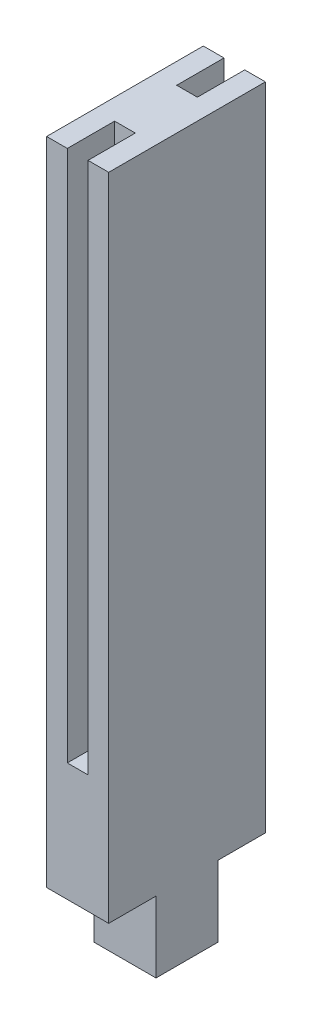
SolidWorks part; units mm, degrees
ref_plane "Front Plane" through (0, 0, 0) normal (0, 0, 1) x (1, 0, 0)
ref_plane "Top Plane" through (0, 0, 0) normal (0, 1, 0) x (1, 0, 0)
ref_plane "Right Plane" through (0, 0, 0) normal (1, 0, 0) x (0, 0, -1)
sketch "Sketch1" plane through (0, 0, 0) normal (0, 1, 0) x (1, 0, 0)
  line L1 (-2.625, -2.625) -> (2.625, -2.625)
  line L2 (-2.625, -2.625) -> (-2.625, 2.625)
  line L3 (-2.625, 2.625) -> (2.625, 2.625)
  line L4 (2.625, -2.625) -> (2.625, 2.625)
  line L5 (-2.625, -2.625) -> (2.625, 2.625) construction
  line L6 (-2.625, 2.625) -> (2.625, -2.625) construction
  point P0 (0, 0)
  dimension "D1" = 5.25
  dimension "D2" = 5.25
extrude "Boss-Extrude1" add sketch "Sketch1" along normal blind 6
sketch "Sketch2" plane through (0, 6, 0) normal (0, 1, 0) x (1, 0, 0)
  line L1 (-2.625, 2.625) -> (2.625, 2.625)
  line L2 (-2.625, 2.625) -> (-2.625, -6.625)
  line L3 (-2.625, -6.625) -> (2.625, -6.625)
  line L4 (2.625, 2.625) -> (2.625, -6.625)
  dimension "D1" = 5.25
  dimension "D2" = 9.25
extrude "Boss-Extrude2" add sketch "Sketch2" along normal blind 55
sketch "Sketch3" plane through (0, 61, 0) normal (0, 1, 0) x (1, 0, 0)
  line L0 (-2.625, -6.625) -> (2.625, -6.625) construction
  line L1 (-0.875, -10.625) -> (0.875, -10.625)
  line L2 (-0.875, -10.625) -> (-0.875, -2.625)
  line L3 (-0.875, -2.625) -> (0.875, -2.625)
  line L4 (0.875, -10.625) -> (0.875, -2.625)
  line L5 (-0.875, -10.625) -> (0.875, -2.625) construction
  line L6 (-0.875, -2.625) -> (0.875, -10.625) construction
  point P0 (0, -6.625)
  dimension "D1" = 1.75
  dimension "D2" = 4
extrude "Cut-Extrude1" cut sketch "Sketch3" against normal blind 45
sketch "Sketch4" plane through (0, 0, -2.625) normal (0, 0, -1) x (-1, 0, 0)
  line L0 (2.625, 61) -> (2.625, 0) construction
  line L1 (-2.625, 61) -> (2.625, 61)
  line L2 (-2.625, 61) -> (-2.625, 6)
  line L3 (-2.625, 6) -> (2.625, 6)
  line L4 (2.625, 61) -> (2.625, 6)
  dimension "D1" = 55
extrude "Boss-Extrude3" add sketch "Sketch4" along normal blind 4
sketch "Sketch5" plane through (0, 61, 0) normal (0, 1, 0) x (1, 0, 0)
  line L0 (-2.625, 6.625) -> (2.625, 6.625) construction
  line L1 (-0.875, 10.625) -> (0.875, 10.625)
  line L2 (-0.875, 10.625) -> (-0.875, 2.625)
  line L3 (-0.875, 2.625) -> (0.875, 2.625)
  line L4 (0.875, 10.625) -> (0.875, 2.625)
  line L5 (-0.875, 10.625) -> (0.875, 2.625) construction
  line L6 (-0.875, 2.625) -> (0.875, 10.625) construction
  point P0 (0, 6.625)
  dimension "D1" = 1.75
  dimension "D2" = 4
extrude "Cut-Extrude2" cut sketch "Sketch5" against normal blind 45
